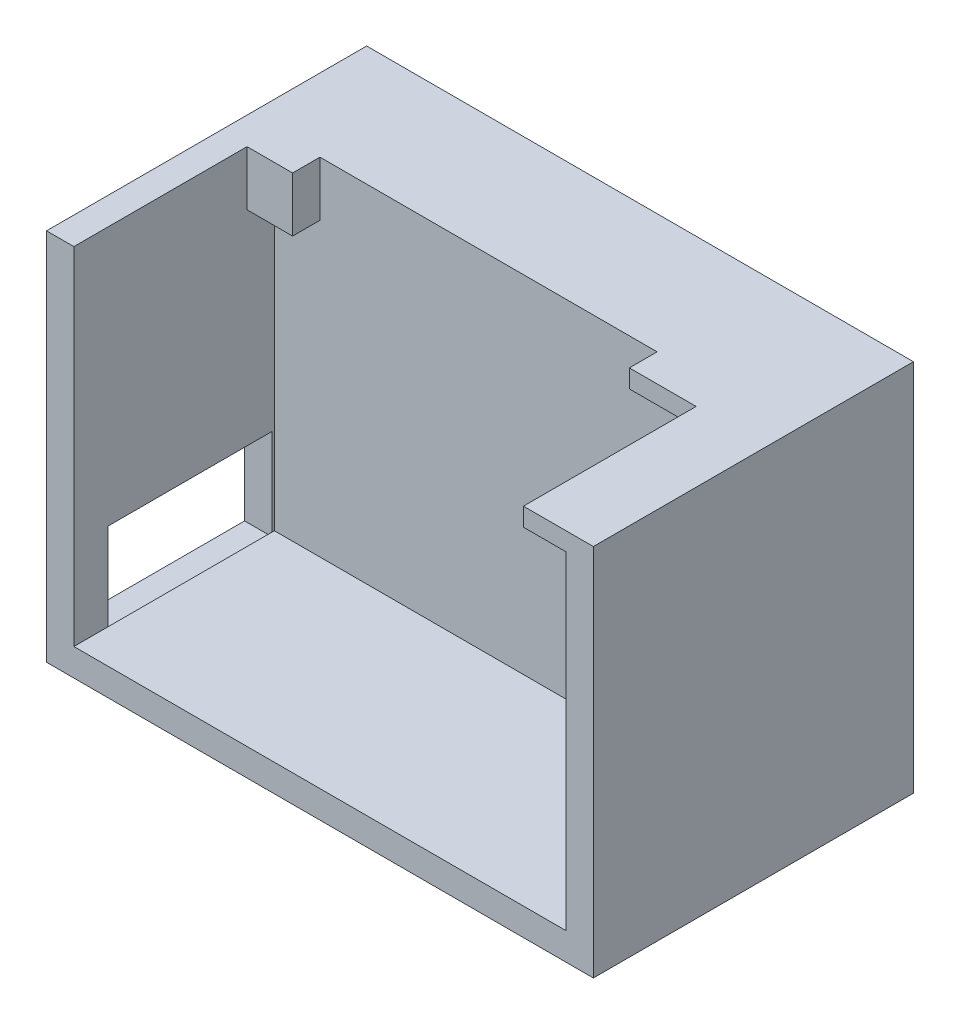
SolidWorks part; units mm, degrees
ref_plane "Plan de face" through (0, 0, 0) normal (0, 0, 1) x (1, 0, 0)
ref_plane "Plan de dessus" through (0, 0, 0) normal (0, 1, 0) x (1, 0, 0)
ref_plane "Plan de droite" through (0, 0, 0) normal (1, 0, 0) x (0, 0, -1)
sketch "Esquisse1" plane through (0, 0, 0) normal (0, 0, 1) x (1, 0, 0)
  line L1 (0, 0) -> (60, 0)
  line L2 (0, 0) -> (0, 42)
  line L3 (0, 42) -> (60, 42)
  line L4 (60, 0) -> (60, 42)
  dimension "D1" = 60
  dimension "D2" = 42
extrude "Boss.-Extru.1" add sketch "Esquisse1" along normal blind 35.125
shell "Coque4" thickness 3
ref_plane "Plan1" through (0, 0, 35.125) normal (1, 0, 0) x (0, 0, -1)
sketch "Esquisse7" plane through (0, 0, 3) normal (0, 0, 1) x (1, 0, 0)
  line L1 (3, 39) -> (57, 39)
  line L2 (3, 39) -> (3, 3)
  line L3 (3, 3) -> (57, 3)
  line L4 (57, 39) -> (57, 3)
extrude "Boss.-Extru.2" add sketch "Esquisse7" along normal blind 10.125
sketch "Esquisse8" plane through (0, 42, 0) normal (0, 1, 0) x (1, 0, 0)
  line L1 (0, 0) -> (60, 0)
  line L2 (0, 0) -> (0, -35.125)
  line L3 (0, -35.125) -> (60, -35.125)
  line L4 (60, 0) -> (60, -35.125)
extrude "Enlèv. mat.-Extru.1" cut sketch "Esquisse8" against normal blind 1
sketch "Esquisse9" plane through (0, 41, 0) normal (0, 1, 0) x (1, 0, 0)
  line L0 (57, -13.125) -> (3, -13.125) construction
  line L1 (60, -35.125) -> (50, -35.125)
  line L2 (60, -35.125) -> (60, -13.125)
  line L3 (60, -13.125) -> (50, -13.125)
  line L4 (50, -35.125) -> (50, -13.125)
  dimension "D1" = 10
extrude "Boss.-Extru.3" add sketch "Esquisse9" against normal blind 1
sketch "Esquisse10" plane through (0, 0, 0) normal (-1, 0, 0) x (0, 0, 1)
  line L1 (13.3951, 12.5683) -> (31.3951, 12.5683)
  line L2 (13.3951, 12.5683) -> (13.3951, 2.5683)
  line L3 (13.3951, 2.5683) -> (31.3951, 2.5683)
  line L4 (31.3951, 12.5683) -> (31.3951, 2.5683)
  dimension "D1" = 18
  dimension "D2" = 10
extrude "Enlèv. mat.-Extru.2" cut sketch "Esquisse10" against normal blind 3
sketch "Esquisse13" plane through (0, 39, 0) normal (0, -1, 0) x (-1, 0, 0)
  line L0 (-57, -13.125) -> (-3, -13.125) construction
  line L1 (-3, -35.125) -> (-45, -35.125)
  line L2 (-3, -35.125) -> (-3, -13.125)
  line L3 (-3, -13.125) -> (-45, -13.125)
  line L4 (-45, -35.125) -> (-45, -13.125)
  dimension "D1" = 42
extrude "Enlèv. mat.-Extru.3" cut sketch "Esquisse13" against normal blind 10
ref_plane "Plan2" through (3, 3, 13.125) normal (0, -1, 0) x (-1, 0, 0)
sketch "Esquisse15" plane through (0, 41, 0) normal (0, 1, 0) x (1, 0, 0)
  line L1 (45, -35.125) -> (52.3263, -35.125)
  line L2 (45, -35.125) -> (45, -16.1742)
  line L3 (45, -16.1742) -> (52.3263, -16.1742)
  line L4 (52.3263, -35.125) -> (52.3263, -16.1742)
extrude "Enlèv. mat.-Extru.4" cut sketch "Esquisse15" against normal blind 4
sketch "Esquisse16" plane through (0, 0, 13.125) normal (0, 0, 1) x (1, 0, 0)
  line L1 (3, 41) -> (8, 41)
  line L2 (3, 41) -> (3, 35)
  line L3 (3, 35) -> (8, 35)
  line L4 (8, 41) -> (8, 35)
  dimension "D1" = 6
  dimension "D2" = 5
extrude "Boss.-Extru.4" add sketch "Esquisse16" along normal blind 3
